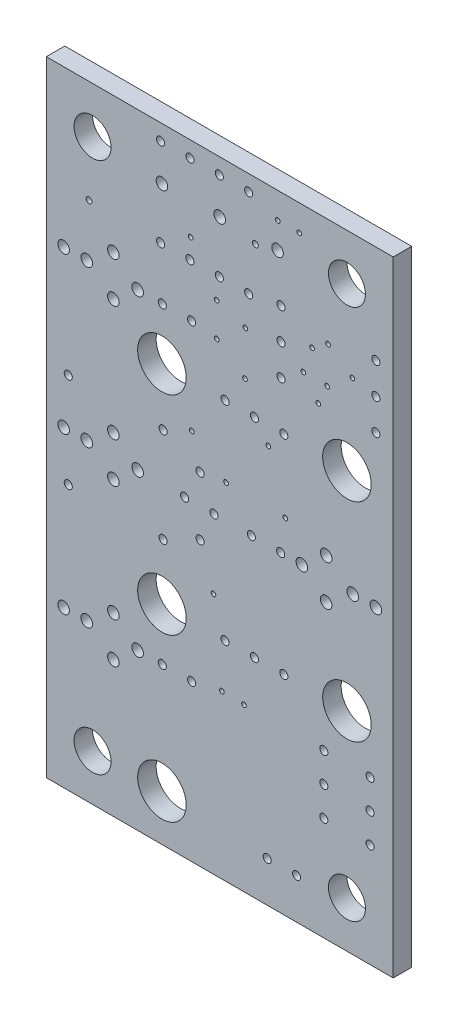
SolidWorks part; units mm, degrees
ref_plane "Plan de face" through (0, 0, 0) normal (0, 0, 1) x (1, 0, 0)
ref_plane "Plan de dessus" through (0, 0, 0) normal (0, 1, 0) x (1, 0, 0)
ref_plane "Plan de droite" through (0, 0, 0) normal (1, 0, 0) x (0, 0, -1)
sketch "Model" plane through (0, 0, 0) normal (0, 0, 1) x (1, 0, 0)
  line L1 (0, 54) -> (30, 54)
  line L2 (0, 54) -> (0, 0)
  line L3 (0, 0) -> (30, 0)
  line L4 (30, 54) -> (30, 0)
  line L444 (-3.697, 0) -> (52.8935, 0) construction
  line L445 (0, -2.1527) -> (0, 78.5143) construction
  line L446 (-3.697, 54) -> (52.8935, 54) construction
  line L447 (30, -2.1527) -> (30, 78.5143) construction
  line L448 (35.6883, 27) -> (41.4743, 27) construction
  line L449 (15, 69.4577) -> (15, 59.6136) construction
  line L450 (4, 57.654) -> (4, 48.7217) construction
  line L451 (-2.7037, 50) -> (5.4842, 50) construction
  circle A0 centre (10, 4.0005) radius 2.1
  circle A1 centre (10, 18.001) radius 2.1
  circle A2 centre (25.9994, 18.001) radius 2.1
  circle A3 centre (10, 35.9994) radius 2.1
  circle A4 centre (25.9994, 35.9994) radius 2.1
  circle A5 centre (10.1003, 22.9006) radius 0.35
  circle A6 centre (19.2024, 34.4475) radius 0.2
  circle A7 centre (23.9992, 8.9611) radius 0.35
  circle A8 centre (28.0005, 14.0411) radius 0.35
  circle A9 centre (27.9992, 8.9611) radius 0.35
  circle A10 centre (7.8994, 27.0002) radius 0.5
  circle A11 centre (12.5705, 40.5003) radius 0.35
  circle A12 centre (21.6446, 3.5001) radius 0.35
  circle A13 centre (19.1046, 3.5001) radius 0.35
  circle A14 centre (17.9997, 18.001) radius 0.35
  circle A15 centre (15.4597, 18.001) radius 0.35
  circle A16 centre (26.5013, 27.0002) radius 0.5
  circle A17 centre (24.2011, 25.2503) radius 0.5
  circle A18 centre (20.2705, 27.0002) radius 0.35
  circle A19 centre (12.5832, 32.2682) radius 0.2
  circle A20 centre (10.0292, 13.5001) radius 0.35
  circle A21 centre (1.4986, 13.5014) radius 0.5
  circle A22 centre (3.4986, 13.5014) radius 0.5
  circle A23 centre (7.8986, 13.5014) radius 0.5
  circle A24 centre (5.7986, 11.7514) radius 0.5
  circle A25 centre (5.7986, 15.2514) radius 0.5
  circle A26 centre (10.1003, 31.0998) radius 0.35
  circle A27 centre (17.1856, 38.4835) radius 0.2
  circle A28 centre (1.8999, 22.8994) radius 0.35
  circle A29 centre (10.0305, 40.5003) radius 0.35
  circle A30 centre (1.8999, 31.0998) radius 0.35
  circle A31 centre (1.4994, 27.0002) radius 0.5
  circle A32 centre (3.4994, 27.0002) radius 0.5
  circle A33 centre (5.7994, 25.2502) radius 0.5
  circle A34 centre (5.7994, 28.7502) radius 0.5
  circle A35 centre (11.9596, 27.0002) radius 0.35
  circle A36 centre (14.4996, 27.0002) radius 0.35
  circle A37 centre (15.4597, 35.9994) radius 0.35
  circle A38 centre (28.5001, 42.799) radius 0.35
  circle A39 centre (28.5001, 40.099) radius 0.35
  circle A40 centre (12.4231, 45.0037) radius 0.35
  circle A41 centre (28.5001, 45.499) radius 0.35
  circle A42 centre (14.9631, 45.0037) radius 0.35
  circle A43 centre (17.5031, 45.0037) radius 0.35
  circle A44 centre (14.9631, 52.6237) radius 0.35
  circle A45 centre (12.4231, 52.6237) radius 0.35
  circle A46 centre (9.8831, 52.6237) radius 0.35
  circle A47 centre (15, 49.4995) radius 0.5
  circle A48 centre (24.3637, 44.6507) radius 0.2
  circle A49 centre (1.4986, 40.5016) radius 0.5
  circle A50 centre (28.5013, 27.0002) radius 0.5
  circle A51 centre (7.8986, 40.5016) radius 0.5
  circle A52 centre (3.4986, 40.5016) radius 0.5
  circle A53 centre (5.7986, 38.7516) radius 0.5
  circle A54 centre (5.7986, 42.2516) radius 0.5
  circle A55 centre (20.0245, 51.7474) radius 0.2
  circle A71 centre (13.2994, 24.4602) radius 0.35
  circle A72 centre (24.0005, 14.0411) radius 0.35
  circle A84 centre (20.3009, 45.499) radius 0.35
  circle A93 centre (12.4905, 46.7335) radius 0.2
  circle A94 centre (3.697, 45.0977) radius 0.25
  circle A129 centre (12.5692, 13.5001) radius 0.35
  circle A132 centre (17.2187, 42.3037) radius 0.2
  circle A139 centre (20.2997, 42.799) radius 0.35
  circle A141 centre (17.7305, 27.0002) radius 0.35
  circle A144 centre (15.5435, 29.8831) radius 0.2
  circle A154 centre (20.3009, 40.099) radius 0.35
  circle A157 centre (27.9997, 11.5011) radius 0.35
  circle A216 centre (26.4732, 43.18) radius 0.2
  circle A217 centre (21.8745, 51.7474) radius 0.2
  circle A226 centre (17.5031, 52.6237) radius 0.35
  circle A227 centre (15.1892, 14.0767) radius 0.2
  circle A228 centre (14.4577, 21.0007) radius 0.2
  circle A238 centre (23.9992, 11.5011) radius 0.35
  circle A239 centre (17.0993, 14.0132) radius 0.2
  circle A241 centre (20.5397, 18.001) radius 0.35
  circle A267 centre (23.5242, 39.8043) radius 0.2
  circle A290 centre (22.1018, 27.0002) radius 0.5
  circle A292 centre (18.0823, 48.9991) radius 0.254
  circle A293 centre (22.2326, 41.496) radius 0.2
  circle A300 centre (14.7383, 40.2336) radius 0.2
  circle A301 centre (14.7383, 43.1317) radius 0.2
  circle A310 centre (10, 49.4995) radius 0.5
  circle A313 centre (17.9997, 35.9994) radius 0.35
  circle A325 centre (9.8831, 45.0037) radius 0.35
  circle A344 centre (20, 49.4995) radius 0.5
  circle A348 centre (24.2824, 41.468) radius 0.2
  circle A349 centre (22.9819, 43.6905) radius 0.2
  circle A364 centre (20.6718, 29.7891) radius 0.2
  circle A366 centre (24.2011, 28.7503) radius 0.5
  circle A380 centre (13.2994, 29.5402) radius 0.35
  circle A387 centre (20.5397, 35.9994) radius 0.35
  circle A388 centre (4, 50) radius 1.6
  circle A389 centre (26, 50) radius 1.6
  circle A390 centre (4, 4) radius 1.6
  circle A391 centre (26, 4) radius 1.6
  dimension "D7" = 2
  dimension "D9" = 2
  dimension "D12" = 2
  dimension "D11" = 2
  dimension "D14" = 2
  dimension "D15" = 2
  dimension "D16" = 2
  dimension "D17" = 2
  dimension "D24" = 2
  dimension "D25" = 2
  dimension "D1" = 30
  dimension "D2" = 54
  dimension "D3" = 27
  dimension "D4" = 15
  dimension "D5" = 4
  dimension "D6" = 4
  dimension "D8" = 2
  dimension "D10" = 3
  dimension "D13" = 2
  dimension "D18" = 2
  dimension "D19" = 3
  dimension "D20" = 4
  dimension "D21" = 2
  dimension "D22" = 4
  dimension "D23" = 2
  dimension "D26" = 2
extrude "Boss.-Extru.1" add sketch "Model" along normal blind 1.6
